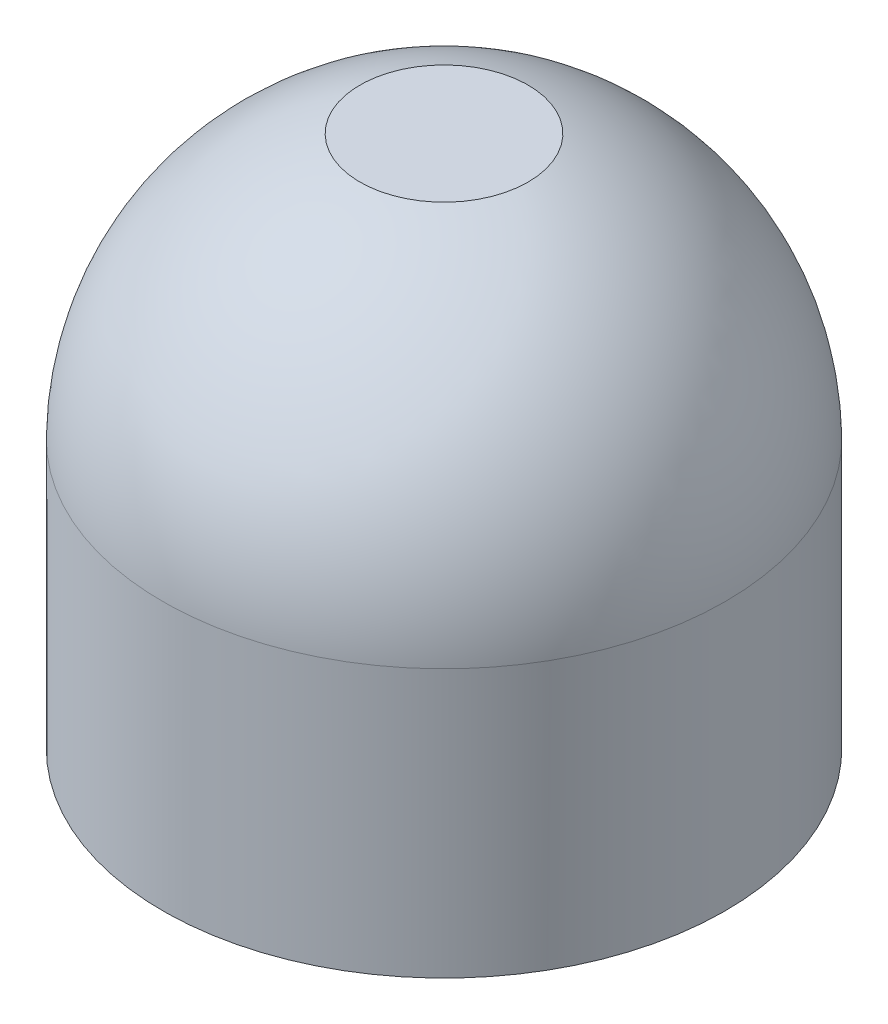
SolidWorks part; units mm, degrees
ref_plane "Front Plane" through (0, 0, 0) normal (0, 0, 1) x (1, 0, 0)
ref_plane "Top Plane" through (0, 0, 0) normal (0, 1, 0) x (1, 0, 0)
ref_plane "Right Plane" through (0, 0, 0) normal (1, 0, 0) x (0, 0, -1)
sketch "Sketch1" plane through (0, 0, 0) normal (0, 1, 0) x (1, 0, 0)
  circle A0 centre (0, 0) radius 5.25
  circle A1 centre (0, 0) radius 4.5
  point P5 (0, 0)
  dimension "D1" = 10.5
  dimension "D2" = 9
extrude "Boss-Extrude1" add sketch "Sketch1" along normal blind 5
sketch "Sketch2" plane through (0, 0, 0) normal (0, 1, 0) x (1, 0, 0)
  line L1 (1.3277, 3.7956) -> (1.3277, 5.7011)
  line L2 (1.3277, 5.7011) -> (-1.5, 5.7011)
  line L3 (-1.5, 5.7011) -> (-1.5, 3.7011)
  line L4 (-1.5, 3.7011) -> (1.3277, 3.7956)
extrude "Cut-Extrude1" cut sketch "Sketch2" along normal blind 5
sketch "Sketch4" plane through (0, 0, 0) normal (0, 0, 1) x (1, 0, 0)
  line L0 (5.25, 5) -> (0, 5)
  line L1 (0, 5) -> (0, 10.18)
  arc A0 (0, 10.18) -> (5.25, 5) centre (0, 4.9295) cw
  dimension "D2" = 5.18
  dimension "D3" = 5.25
revolve "Revolve1" add sketch "Sketch4" angle 360 about L1
ref_plane "Plane1" through (0, 5, 0) normal (0, -1, 0) x (-1, 0, 0)
sketch "Sketch5" plane through (0, 5, 0) normal (0, -1, 0) x (-1, 0, 0)
  line L2 (1.5, 3.4369) -> (1.5, 6)
  line L3 (1.5, 6) -> (-1.3277, 6)
  line L4 (-1.3277, 3.5071) -> (-1.3277, 6)
  arc A0 (-1.3277, 3.5071) -> (1.5, 3.4369) centre (0, 0) ccw
extrude "Cut-Extrude2" cut sketch "Sketch5" against normal blind 2
ref_plane "Plane2" through (0, 10.29, 0) normal (0, -1, 0) x (-1, 0, 0)
sketch "Sketch6" plane through (0, 10.29, 0) normal (0, -1, 0) x (-1, 0, 0)
  circle A0 centre (0, 0) radius 2
extrude "Cut-Extrude4" cut sketch "Sketch6" along normal blind 0.35
